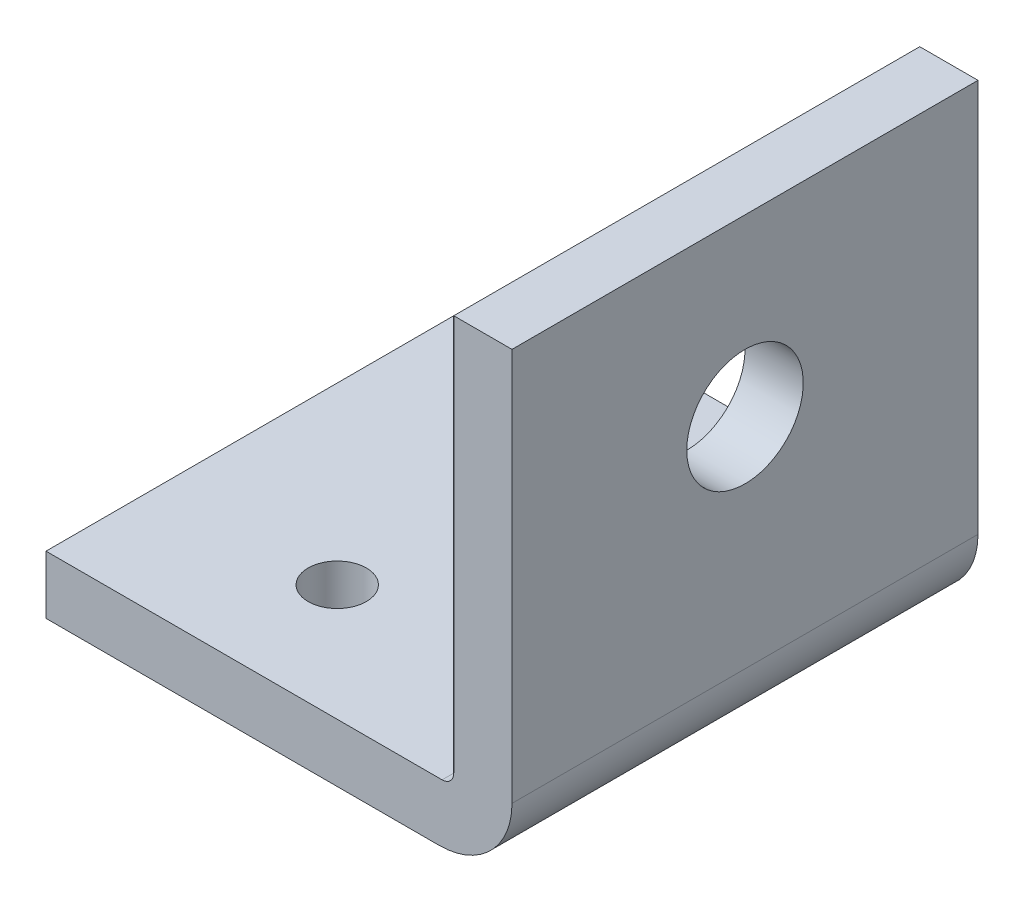
SolidWorks part; units mm, degrees
ref_plane "Front Plane" through (0, 0, 0) normal (0, 0, 1) x (1, 0, 0)
ref_plane "Top Plane" through (0, 0, 0) normal (0, 1, 0) x (1, 0, 0)
ref_plane "Right Plane" through (0, 0, 0) normal (1, 0, 0) x (0, 0, -1)
sketch "Sketch1" plane through (0, 0, 0) normal (0, 0, 1) x (1, 0, 0)
  line L0 (0, 0) -> (0, 5)
  line L1 (0, 5) -> (35, 5)
  line L2 (35, 5) -> (35, 40)
  line L3 (35, 40) -> (40, 40)
  line L4 (40, 40) -> (40, 6.25)
  line L5 (33.75, 0) -> (0, 0)
  arc A0 (40, 6.25) -> (33.75, 0) centre (33.75, 6.25) cw
  point P9 (40, 0)
  dimension "D5" = 6.25
  dimension "D1" = 5
  dimension "D2" = 5
  dimension "D3" = 40
  dimension "D4" = 40
extrude "Boss-Extrude1" add sketch "Sketch1" along normal blind 40
sketch "Sketch3" plane through (0, 5, 0) normal (0, 1, 0) x (1, 0, 0)
  line L0 (35, 0) -> (0, 0) construction
  line L1 (35, -40) -> (0, -40) construction
  line L2 (0, -40) -> (0, 0) construction
  circle A0 centre (15, -10) radius 2.5
  circle A1 centre (15, -30) radius 2.5
  point P8 (0, 0)
  dimension "D1" = 10
  dimension "D4" = 5
  dimension "D2" = 10
  dimension "D3" = 15
extrude "Cut-Extrude1" cut sketch "Sketch3" against normal through all
sketch "Sketch4" plane through (35, 0, 0) normal (-1, 0, 0) x (0, 0, 1)
  line L0 (0, 40) -> (0, 5) construction
  line L1 (40, 40) -> (0, 40) construction
  circle A0 centre (20, 25) radius 5
  dimension "D1" = 20
  dimension "D3" = 10
  dimension "D2" = 15
extrude "Cut-Extrude2" cut sketch "Sketch4" against normal through all
fillet "Fillet1" radius 1 1 edges at (35, 5, 20)
